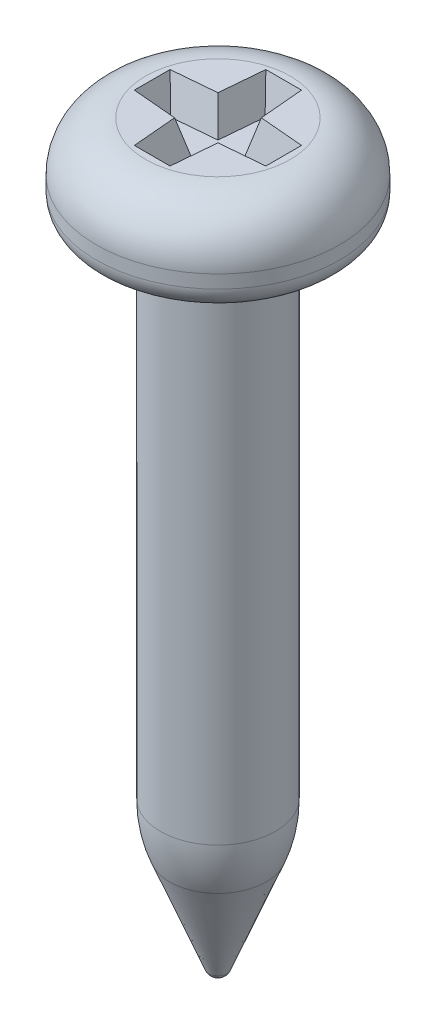
SolidWorks part; units mm, degrees
ref_plane "Front Plane" through (0, 0, 0) normal (0, 0, 1) x (1, 0, 0)
ref_plane "Top Plane" through (0, 0, 0) normal (0, 1, 0) x (1, 0, 0)
ref_plane "Right Plane" through (0, 0, 0) normal (1, 0, 0) x (0, 0, -1)
sketch "Sketch1" plane through (0, 0, 0) normal (0, 0, 1) x (1, 0, 0)
  line L0 (0, 0) -> (0, -11.3) construction
  line L2 (0.875, -8.9644) -> (0.875, -1.45)
  line L3 (1.025, -1.3) -> (1.5, -1.3)
  line L4 (1.85, -0.95) -> (1.85, -0.75)
  line L5 (1.1, 0) -> (0, 0)
  line L6 (0, 0) -> (0, -11.3)
  line L7 (0.7348, -9.7) -> (0.1395, -11.2052)
  arc A0 (1.85, -0.75) -> (1.1, 0) centre (1.1, -0.75) ccw
  arc A1 (1.5, -1.3) -> (1.85, -0.95) centre (1.5, -0.95) ccw
  arc A2 (0.875, -1.45) -> (1.025, -1.3) centre (1.025, -1.45) cw
  arc A3 (0.1395, -11.2052) -> (0, -11.3) centre (0, -11.15) cw
  arc A4 (0.7348, -9.7) -> (0.875, -8.9644) centre (-1.125, -8.9644) ccw
  point P13 (0.875, -1.3)
  dimension "D3" = 0.75
  dimension "D6" = 0.35
  dimension "D7" = 0.15
  dimension "D8" = 2
  dimension "D4" = 1.6
  dimension "D10" = 0.15
  dimension "D1" = 3.7
  dimension "D2" = 1.3
  dimension "D5" = 1.75
  dimension "D9" = 10
revolve "Revolve1" add sketch "Sketch1" angle 360 about L0
sketch "Sketch2" plane through (0, 0, 0) normal (0, 1, 0) x (1, 0, 0)
  line L0 (0, 1) -> (0, 0) construction
  line L1 (0, 0) -> (1, 0) construction
  line L2 (-0.2714, 1) -> (0.2714, 1)
  line L3 (0.2714, 1) -> (0.33, 0.33)
  line L4 (0.33, 0.33) -> (1, 0.2714)
  line L5 (1, 0.2714) -> (1, -0.2714)
  line L6 (-1, 0.2714) -> (-1, -0.2714)
  line L7 (-0.33, 0.33) -> (-1, 0.2714)
  line L8 (-0.2714, 1) -> (-0.33, 0.33)
  line L9 (-0.33, -0.33) -> (-1, -0.2714)
  line L10 (-0.2714, -1) -> (-0.33, -0.33)
  line L11 (-0.2714, -1) -> (0.2714, -1)
  line L12 (0.2714, -1) -> (0.33, -0.33)
  line L13 (0.33, -0.33) -> (1, -0.2714)
  point P18 (-1, 0)
  point P26 (0, 0)
  dimension "D1" = 95
  dimension "D2" = 2
  dimension "D3" = 0.66
extrude "Cut-Extrude1" cut sketch "Sketch2" against normal blind 0.5 draft 15
